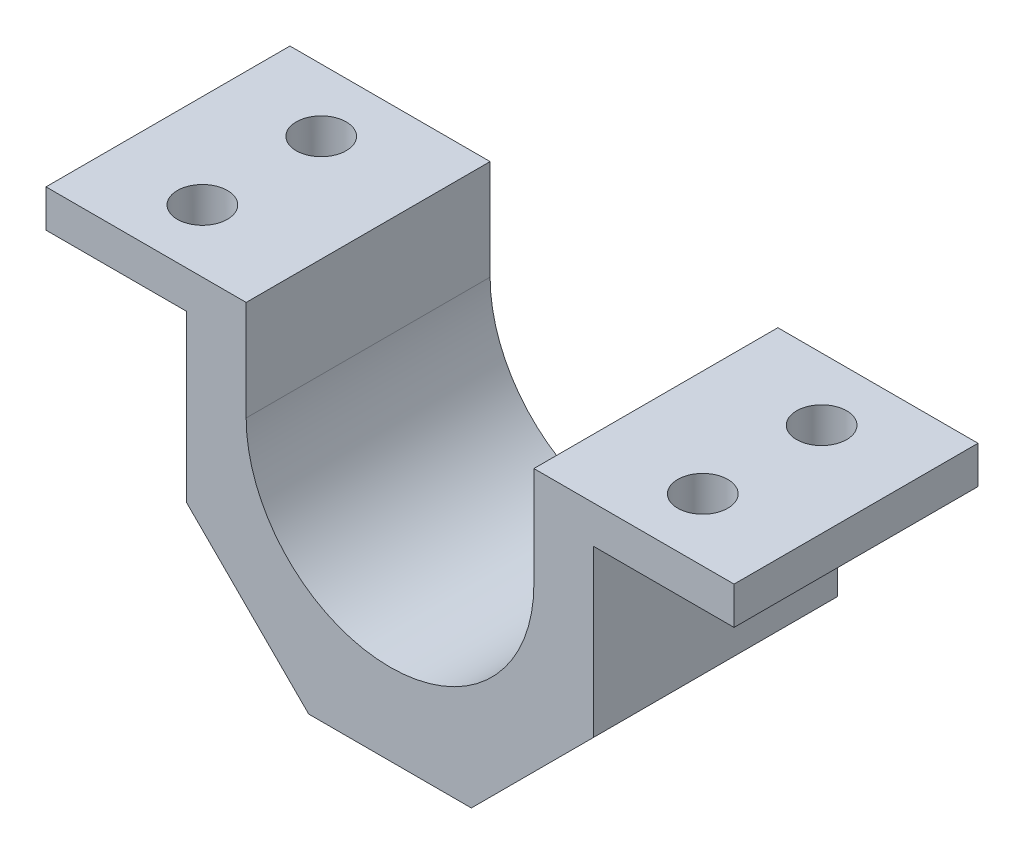
SolidWorks part; units mm, degrees
ref_plane "Front Plane" through (0, 0, 0) normal (0, 0, 1) x (1, 0, 0)
ref_plane "Top Plane" through (0, 0, 0) normal (0, 1, 0) x (1, 0, 0)
ref_plane "Right Plane" through (0, 0, 0) normal (1, 0, 0) x (0, 0, -1)
sketch "Sketch1" plane through (0, 0, 0) normal (0, 0, 1) x (1, 0, 0)
  line L0 (-55, 16) -> (-23, 16)
  line L1 (-13, -36) -> (13, -36)
  line L2 (-55, 16) -> (-55, 10)
  line L3 (-55, 10) -> (-32.5, 10)
  line L4 (-32.5, 10) -> (-32.5, -16.5)
  line L5 (-32.5, -16.5) -> (-13, -36)
  line L6 (13, -36) -> (32.5, -16.5)
  line L7 (32.5, -16.5) -> (32.5, 10)
  line L8 (32.5, 10) -> (55, 10)
  line L9 (55, 10) -> (55, 16)
  line L10 (-23, 0) -> (-23, 16)
  line L11 (23, 0) -> (23, 16)
  line L12 (23, 16) -> (55, 16)
  arc A0 (-23, 0) -> (23, 0) centre (0, 0) ccw
  dimension "D12" = 46
  dimension "D1" = 16
  dimension "D2" = 26
  dimension "D3" = 52
  dimension "D4" = 110
  dimension "D5" = 6
  dimension "D6" = 6
  dimension "D7" = 32.5
  dimension "D8" = 32.5
  dimension "D9" = 45
  dimension "D10" = 45
  dimension "D11" = 55
extrude "Boss-Extrude1" add sketch "Sketch1" along normal mid plane 39
sketch "Sketch2" plane through (0, 16, 0) normal (0, 1, 0) x (1, 0, 0)
  line L0 (40, -33.6637) -> (40, 33.6637) construction
  line L1 (0, 0) -> (60.5827, 0) construction
  line L2 (0, -21.45) -> (0, 21.45) construction
  circle A0 centre (40, 9.5) radius 4
  circle A1 centre (40, -9.5) radius 4
  circle A2 centre (-40, -9.5) radius 4
  circle A3 centre (-40, 9.5) radius 4
  point P3 (40, 0)
  dimension "D4" = 8
  dimension "D5" = 8
  dimension "D1" = 40
  dimension "D2" = 9.5
  dimension "D3" = 9.5
extrude "Cut-Extrude1" cut sketch "Sketch2" against normal blind 39
